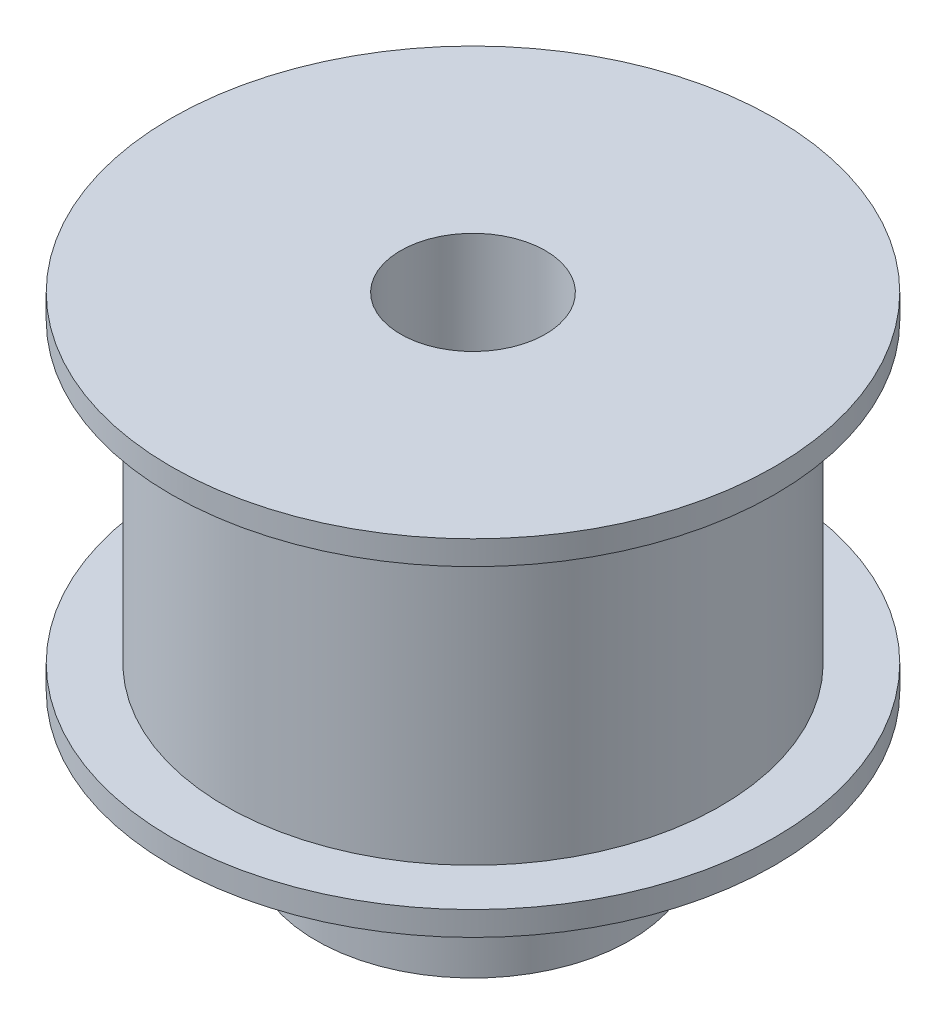
SolidWorks part; units mm, degrees
ref_plane "Front Plane" through (0, 0, 0) normal (0, 0, 1) x (1, 0, 0)
ref_plane "Top Plane" through (0, 0, 0) normal (0, 1, 0) x (1, 0, 0)
ref_plane "Right Plane" through (0, 0, 0) normal (1, 0, 0) x (0, 0, -1)
sketch "Sketch2" plane through (0, 0, 0) normal (0, 0, 1) x (1, 0, 0)
  line L0 (0, 0) -> (0, 90.1897) construction
  line L1 (6.5, 0) -> (0, 0)
  line L2 (0, 0) -> (0, 20)
  line L3 (6.5, 5.7) -> (6.5, 0)
  line L4 (12.5, 5.7) -> (12.5, 6.7)
  line L5 (12.5, 6.7) -> (10.255, 6.7)
  line L6 (10.255, 6.7) -> (10.255, 19)
  line L7 (10.255, 19) -> (12.5, 19)
  line L8 (6.5, 5.7) -> (12.5, 5.7)
  line L9 (12.5, 19) -> (12.5, 20)
  line L10 (12.5, 20) -> (0, 20)
  dimension "D1" = 20.51
  dimension "D2" = 13
  dimension "D3" = 14.3
  dimension "D4" = 20
  dimension "D5" = 25
  dimension "D6" = 1
revolve "Revolve1" add sketch "Sketch2" angle 360 about L0
sketch "Sketch3" plane through (0, 0, 0) normal (0, -1, 0) x (1, 0, 0)
  circle A0 centre (0, 0) radius 3
  dimension "D1" = 6
extrude "Cut-Extrude1" cut sketch "Sketch3" against normal through all
